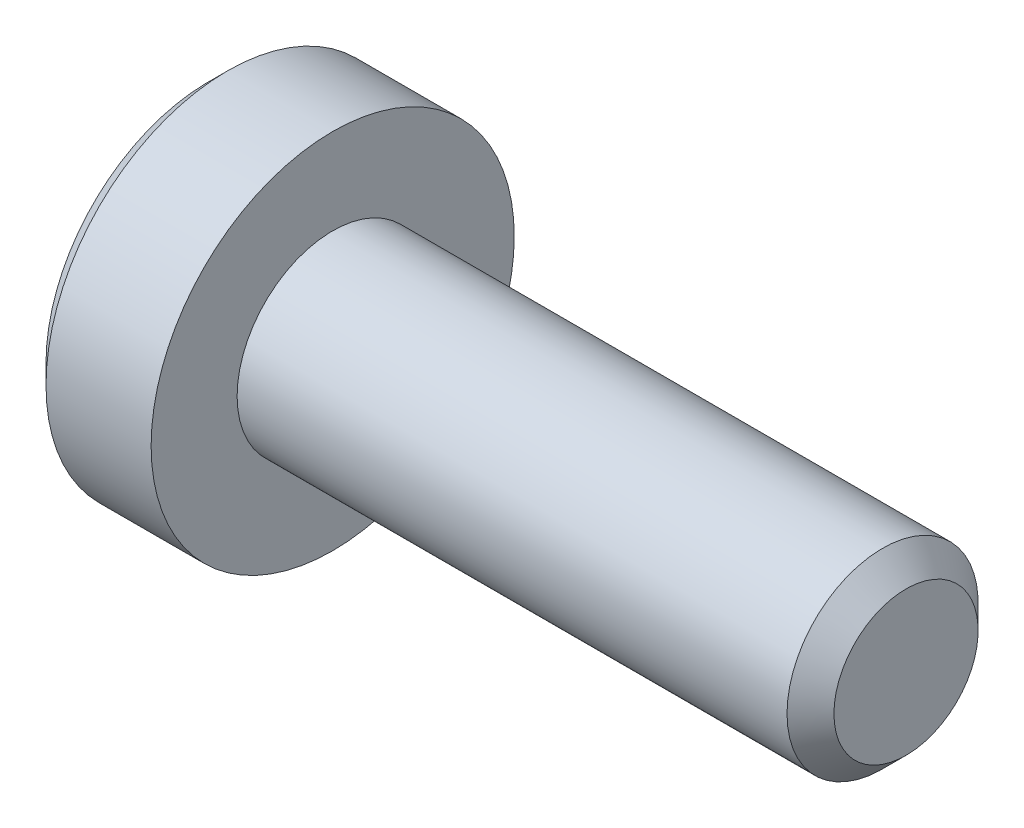
SolidWorks part; units mm, degrees
material "AISI 304"
ref_plane "正面" through (0, 0, 0) normal (0, 0, 1) x (1, 0, 0)
ref_plane "平面" through (0, 0, 0) normal (0, 1, 0) x (1, 0, 0)
ref_plane "右側面" through (0, 0, 0) normal (1, 0, 0) x (0, 0, -1)
ref_plane "Plane1" through (0, 0, 0) normal (0, 0, 1) x (1, 0, 0)
sketch "Sketch1" plane through (0, 0, 0) normal (0, 0, 1) x (1, 0, 0)
  line L0 (-1.3, 0) -> (-1.3, 1.7)
  line L1 (-1.3, 1.7) -> (-1.1, 1.9)
  line L2 (-1.1, 1.9) -> (0, 1.9)
  line L3 (0, 1.9) -> (0, 1)
  line L4 (0, 1) -> (5.7545, 1)
  line L5 (5.7545, 1) -> (6, 0.7545)
  line L6 (6, 0.7545) -> (6, 0)
  line L7 (6, 0) -> (-1.3, 0)
  line L8 (6, 0) -> (-1.3, 0) construction
revolve "Revolve1" add sketch "Sketch1" angle 360 about L8
cosmetic thread "Cosmetic Thread1" parameters "D1"=7.5748, "D2"=1.509
ref_plane "Plane2" through (-1.3, 0, 0) normal (1, 0, 0) x (0, 0, -1)
sketch "Sketch2" plane through (-1.3, 0, 0) normal (1, 0, 0) x (0, 0, -1)
  line L0 (-0.65, -0.3753) -> (0, -0.7506)
  line L1 (0, -0.7506) -> (0.65, -0.3753)
  line L2 (0.65, -0.3753) -> (0.65, 0.3753)
  line L3 (0.65, 0.3753) -> (0, 0.7506)
  line L4 (0, 0.7506) -> (-0.65, 0.3753)
  line L5 (-0.65, 0.3753) -> (-0.65, -0.3753)
extrude "Cut-Extrude1" cut sketch "Sketch2" along normal blind 0.7
